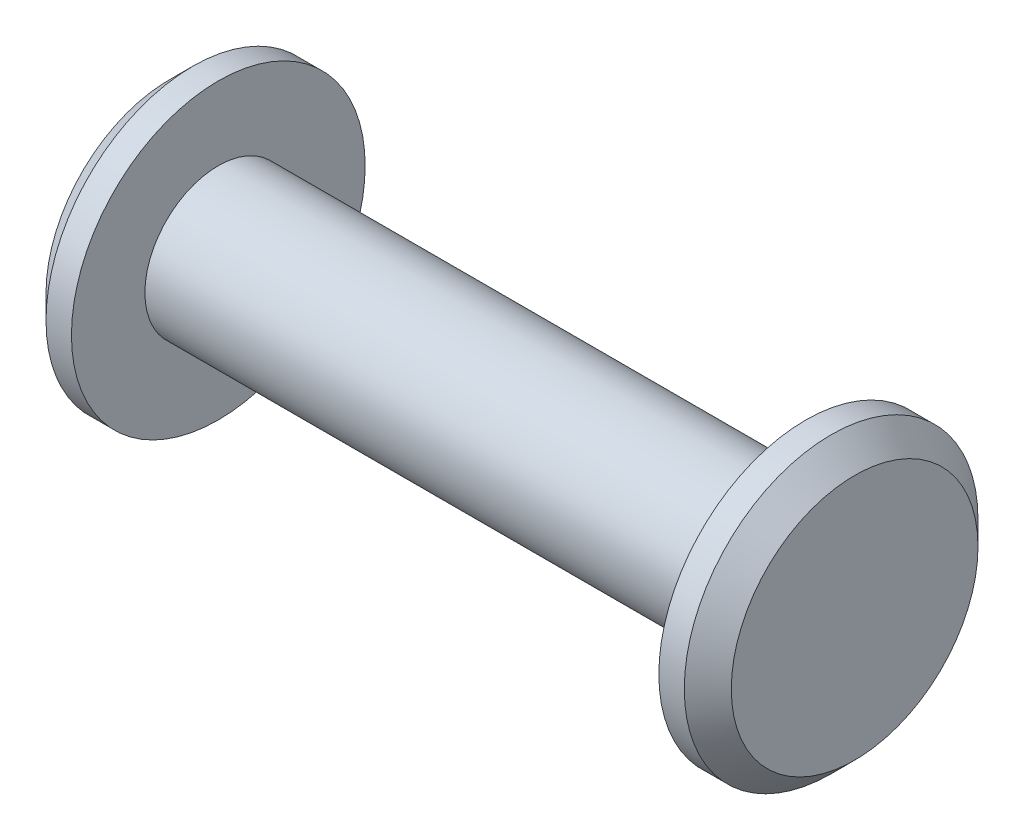
SolidWorks part; units mm, degrees
material "AISI 1015 Steel, Cold Drawn (SS)"
ref_plane "front" through (0, 0, 0) normal (0, 0, 1) x (1, 0, 0)
ref_plane "top" through (0, 0, 0) normal (0, 1, 0) x (1, 0, 0)
ref_plane "side" through (0, 0, 0) normal (1, 0, 0) x (0, 0, -1)
sketch "Sketch1" plane through (0, 0, 0) normal (0, 0, 1) x (1, 0, 0)
  line L0 (0, 0) -> (55.8636, 0) construction
  line L1 (11.1125, 0) -> (11.1125, 4.7625)
  line L2 (11.1125, 4.7625) -> (9.525, 4.7625)
  line L3 (9.525, 4.7625) -> (9.525, 2.3813)
  line L4 (9.525, 2.3813) -> (-9.525, 2.3813)
  line L5 (0, 0) -> (0, 55.2608) construction
  line L6 (-11.1125, 0) -> (11.1125, 0)
  line L7 (-9.525, 4.7625) -> (-9.525, 2.3813)
  line L8 (-11.1125, 4.7625) -> (-9.525, 4.7625)
  line L9 (-11.1125, 0) -> (-11.1125, 4.7625)
  point P12 (11.1125, -4.7625)
  point P13 (9.525, 2.3813)
  point P14 (9.525, -2.3813)
  dimension "D1" = 19.05
  dimension "D2" = 22.225
  dimension "D3" = 4.7625
  dimension "D4" = 9.525
revolve "Base-Revolve" add sketch "Sketch1" angle 360 about L0
chamfer "Chamfer1" distance 0.762 angle 45
